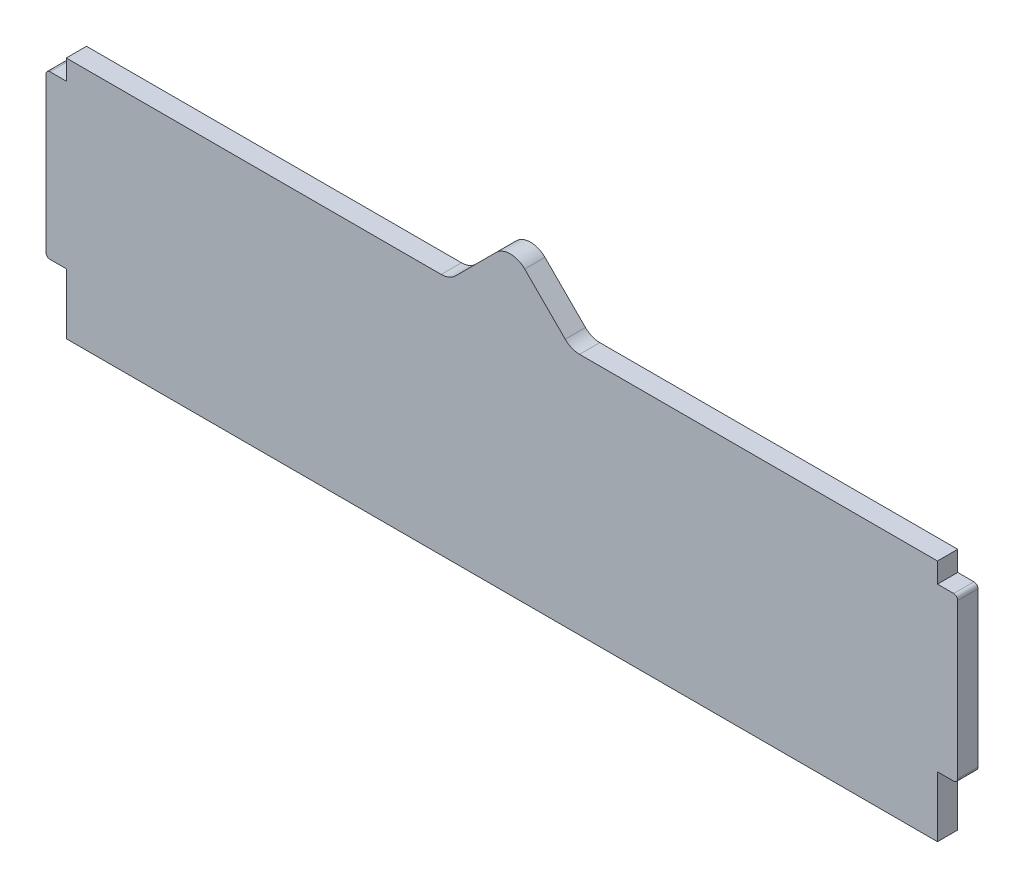
SolidWorks part; units mm, degrees
ref_plane "Front" through (0, 0, 0) normal (0, 0, 1) x (1, 0, 0)
ref_plane "Top" through (0, 0, 0) normal (0, 1, 0) x (1, 0, 0)
ref_plane "Right" through (0, 0, 0) normal (1, 0, 0) x (0, 0, -1)
sketch "Sketch1" plane through (0, 0, 0) normal (0, 0, 1) x (1, 0, 0)
  line L0 (215, 55.05) -> (215, 60)
  line L1 (0, 0) -> (215, 0)
  line L2 (0, 0) -> (0, 14.95)
  line L3 (0, 60) -> (94.5956, 60)
  line L4 (215, 0) -> (215, 14.95)
  line L5 (0, 55.05) -> (-5, 55.05)
  line L7 (0, 14.95) -> (-5, 14.95)
  line L8 (-5, 55.05) -> (-5, 14.95)
  line L9 (215, 55.05) -> (220, 55.05)
  line L11 (215, 14.95) -> (220, 14.95)
  line L12 (220, 55.05) -> (220, 14.95)
  line L13 (0, 55.05) -> (0, 60)
  line L14 (94.5956, 60) -> (109.5956, 75)
  line L15 (109.5956, 75) -> (124.5956, 60)
  line L16 (124.5956, 60) -> (215, 60)
  dimension "D1" = 215
  dimension "D2" = 60
  dimension "D3" = 5
  dimension "D4" = 4.95
  dimension "D5" = 40.1
  dimension "D6" = 4.95
  dimension "D7" = 40.1
  dimension "D8" = 5
  dimension "D9" = 15
  dimension "D10" = 15
extrude "Boss-Extrude1" add sketch "Sketch1" along normal blind 5
fillet "Fillet1" radius 5 3 edges at (94.5956, 60, 2.5) (124.5956, 60, 2.5) (109.5956, 75, 2.5)
fillet "Fillet2" radius 1 4 edges at (-5, 55.05, 2.5) (-5, 14.95, 2.5) (220, 14.95, 2.5) (220, 55.05, 2.5)
